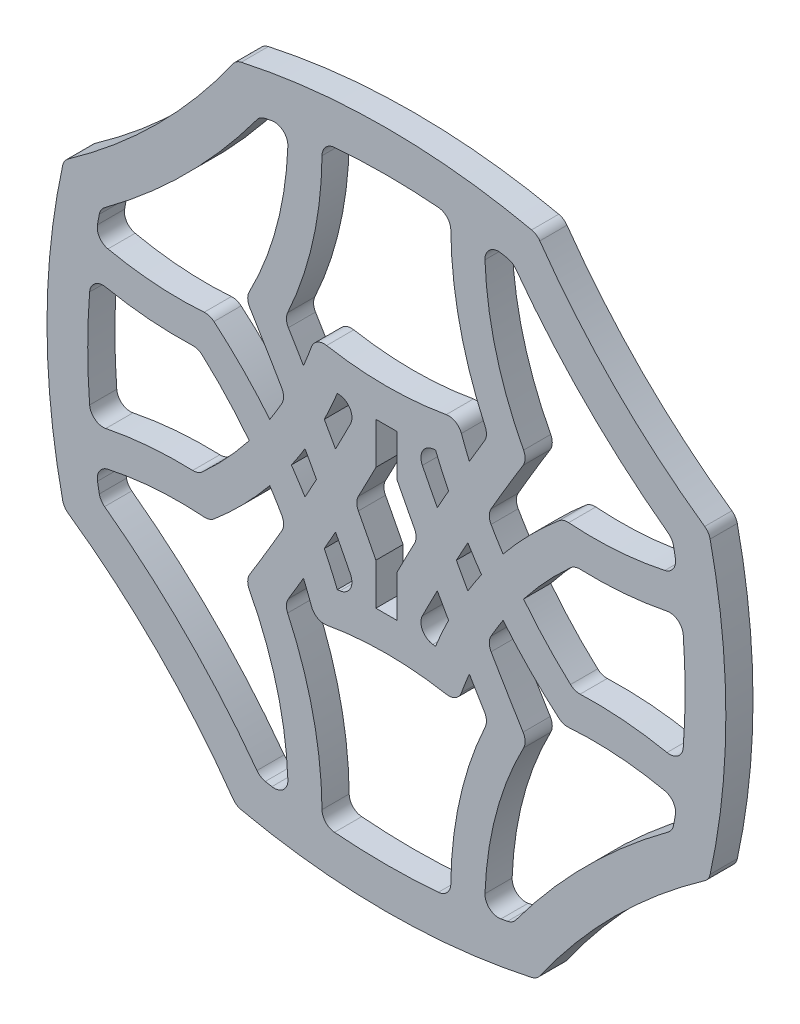
SolidWorks part; units mm, degrees
ref_plane "前视基准面" through (0, 0, 0) normal (0, 0, 1) x (1, 0, 0)
ref_plane "上视基准面" through (0, 0, 0) normal (0, 1, 0) x (1, 0, 0)
ref_plane "右视基准面" through (0, 0, 0) normal (1, 0, 0) x (0, 0, -1)
sketch "草图1" plane through (0, 0, 0) normal (0, 0, 1) x (1, 0, 0)
  line L0 (-3.1552, 0) -> (4.9138, 0) construction
  line L1 (0, 3.8534) -> (0, -1.8879) construction
  line L2 (0.0911, -0.0425) -> (-46.1387, 21.5148) construction
  line L4 (1.55, 12.05) -> (-1.55, 12.05)
  line L5 (1.55, 12.05) -> (1.55, 5.9226)
  line L6 (1.55, -12.05) -> (-1.55, -12.05)
  line L7 (-1.55, 12.05) -> (-1.55, 5.9226)
  line L8 (1.6505, -2.8587) -> (-5.8196, 10.0798) construction
  line L9 (-1.55, 0.7228) -> (-1.55, 0) construction
  line L10 (-1.55, -5.9226) -> (-1.55, -12.05)
  line L11 (-1.55, 2.6847) -> (-1.55, 0.7228) construction
  line L12 (-1.55, 0) -> (-1.55, -5.9226) construction
  line L13 (1.55, -0.7228) -> (1.55, -2.6847) construction
  line L14 (1.55, -5.9226) -> (1.55, -12.05)
  line L15 (1.55, -2.6847) -> (1.55, -5.9226) construction
  line L16 (1.55, 0) -> (1.55, -0.7228) construction
  line L17 (1.55, 5.9226) -> (1.55, 0) construction
  line L18 (-1.55, 5.9226) -> (-1.55, 2.6847) construction
  arc A106 (-22.1564, 47.5146) -> (22.1564, 47.5146) centre (0, -50) cw
  arc A107 (47.5146, 22.1564) -> (47.5146, -22.1564) centre (-50, 0) cw
  arc A108 (22.1564, -47.5146) -> (-22.1564, -47.5146) centre (0, 50) cw
  arc A109 (-47.5146, -22.1564) -> (-47.5146, 22.1564) centre (50, 0) cw
  arc A110 (22.1564, 47.5146) -> (47.5146, 22.1564) centre (104.4001, 104.4001) ccw
  arc A111 (47.5146, -22.1564) -> (22.1564, -47.5146) centre (104.4001, -104.4001) ccw
  arc A112 (-22.1564, -47.5146) -> (-47.5146, -22.1564) centre (-104.4001, -104.4001) ccw
  arc A113 (-47.5146, 22.1564) -> (-22.1564, 47.5146) centre (-104.4001, 104.4001) ccw
  arc A114 (-18.6124, 42.1389) -> (-14.4889, 42.8766) centre (0, -50) cw
  arc A115 (42.1389, 18.6124) -> (42.876, 14.4931) centre (-50, 0) cw
  arc A116 (18.6124, -42.1389) -> (14.4889, -42.8766) centre (0, 50) cw
  arc A117 (-42.1389, -18.6124) -> (-42.876, -14.4931) centre (50, 0) cw
  arc A118 (18.6124, 42.1389) -> (42.1389, 18.6124) centre (104.4001, 104.4001) ccw
  arc A119 (42.1389, -18.6124) -> (18.6124, -42.1389) centre (104.4001, -104.4001) ccw
  arc A120 (-18.6124, -42.1389) -> (-42.1389, -18.6124) centre (-104.4001, -104.4001) ccw
  arc A121 (-42.1389, 18.6124) -> (-18.6124, 42.1389) centre (-104.4001, 104.4001) ccw
  arc A122 (10.4858, 18.1619) -> (-10.4858, 18.1619) centre (0, 67.05) cw
  arc A123 (7.2328, 12.5277) -> (4, 12.1956) centre (0, 67.05) cw
  arc A124 (7.2328, -12.5277) -> (4, -12.1956) centre (0, -67.05) ccw
  arc A125 (10.4858, -18.1619) -> (-10.4858, -18.1619) centre (0, -67.05) ccw
  arc A126 (-10.4858, 18.1619) -> (-12.2188, 13.5572) centre (-67.5025, 36.9924) cw
  arc A127 (-7.2328, 12.5277) -> (-9.1545, 8.244) centre (-67.5025, 36.9924) cw
  arc A128 (-43.5187, -9.5) -> (-27.7384, -8) centre (-30.4783, -62.9317) cw
  arc A129 (-26.0438, -13.1288) -> (-42.876, -14.4931) centre (-30.4783, -62.9317) ccw
  arc A130 (-26.0438, 13.1288) -> (-42.876, 14.4931) centre (-30.4783, 62.9317) cw
  arc A131 (-43.5187, 9.5) -> (-27.7384, 8) centre (-30.4783, 62.9317) ccw
  arc A132 (-7.2328, -12.5277) -> (-9.1545, -8.244) centre (-67.5025, -36.9924) ccw
  arc A133 (-10.4858, -18.1619) -> (-12.2188, -13.5572) centre (-67.5025, -36.9924) ccw
  arc A134 (-20.2049, 0) -> (-27.7384, -8) centre (-67.5025, 36.9924) cw
  arc A135 (-17.1843, 4.2269) -> (-26.0438, 13.1288) centre (-67.5025, -36.9924) ccw
  arc A136 (-20.2049, 0) -> (-27.7384, 8) centre (-67.5025, -36.9924) ccw
  arc A137 (-17.1843, -4.2269) -> (-26.0438, -13.1288) centre (-67.5025, 36.9924) cw
  arc A138 (10.4858, 18.1619) -> (12.2188, 13.5572) centre (67.5025, 36.9924) ccw
  arc A139 (7.2328, 12.5277) -> (9.1545, 8.244) centre (67.5025, 36.9924) ccw
  arc A140 (7.2328, -12.5277) -> (9.1545, -8.244) centre (67.5025, -36.9924) cw
  arc A141 (10.4858, -18.1619) -> (12.2188, -13.5572) centre (67.5025, -36.9924) cw
  arc A142 (17.1843, 4.2269) -> (26.0438, 13.1288) centre (67.5025, -36.9924) cw
  arc A143 (20.2049, 0) -> (27.7384, 8) centre (67.5025, -36.9924) cw
  arc A144 (20.2049, 0) -> (27.7384, -8) centre (67.5025, 36.9924) ccw
  arc A145 (17.1843, -4.2269) -> (26.0438, -13.1288) centre (67.5025, 36.9924) ccw
  arc A146 (43.5187, -9.5) -> (27.7384, -8) centre (30.4783, -62.9317) ccw
  arc A147 (26.0438, -13.1288) -> (42.876, -14.4931) centre (30.4783, -62.9317) cw
  arc A148 (43.5187, 9.5) -> (27.7384, 8) centre (30.4783, 62.9317) cw
  arc A149 (26.0438, 13.1288) -> (42.876, 14.4931) centre (30.4783, 62.9317) ccw
  arc A150 (-43.5187, 9.5) -> (-42.876, 14.4931) centre (50, 0) cw construction
  arc A151 (-42.876, 14.4931) -> (-42.1389, 18.6124) centre (50, 0) cw
  arc A152 (-42.876, -14.4931) -> (-43.5187, -9.5) centre (50, 0) cw construction
  arc A153 (-43.5187, -9.5) -> (-43.5187, 9.5) centre (50, 0) cw
  arc A154 (43.5187, -9.5) -> (42.876, -14.4931) centre (-50, 0) cw construction
  arc A155 (42.876, -14.4931) -> (42.1389, -18.6124) centre (-50, 0) cw
  arc A156 (42.876, 14.4931) -> (43.5187, 9.5) centre (-50, 0) cw construction
  arc A157 (43.5187, 9.5) -> (43.5187, -9.5) centre (-50, 0) cw
  arc A158 (-4, -12.1956) -> (-7.5, -5.2865) centre (-326.3267, -171.1366) ccw
  arc A159 (-1.55, -5.9226) -> (-4.6315, 0) centre (-326.3267, -171.1366) ccw
  arc A160 (-15, 18.2077) -> (-9.5, 43.5187) centre (-64.4845, 42.2136) ccw
  arc A161 (-20.7386, 18) -> (-14.4889, 42.8766) centre (-64.4845, 42.2136) ccw
  arc A162 (1.55, -5.9226) -> (4.6315, 0) centre (326.3267, -171.1366) cw
  arc A163 (4, -12.1956) -> (7.5, -5.2865) centre (326.3267, -171.1366) cw
  arc A164 (20.7386, 18) -> (14.4889, 42.8766) centre (64.4845, 42.2136) cw
  arc A165 (15, 18.2077) -> (9.5, 43.5187) centre (64.4845, 42.2136) cw
  arc A166 (20.7386, -18) -> (14.4889, -42.8766) centre (64.4845, -42.2136) ccw
  arc A167 (15, -18.2077) -> (9.5, -43.5187) centre (64.4845, -42.2136) ccw
  arc A168 (4, 12.1956) -> (7.5, 5.2865) centre (326.3267, 171.1366) ccw
  arc A169 (1.55, 5.9226) -> (4.6315, 0) centre (326.3267, 171.1366) ccw
  arc A170 (-1.55, 5.9226) -> (-4.6315, 0) centre (-326.3267, 171.1366) cw
  arc A171 (-4, 12.1956) -> (-7.5, 5.2865) centre (-326.3267, 171.1366) cw
  arc A172 (-20.7386, -18) -> (-14.4889, -42.8766) centre (-64.4845, -42.2136) cw
  arc A173 (-15, -18.2077) -> (-9.5, -43.5187) centre (-64.4845, -42.2136) cw
  arc A174 (-14.4889, 42.8766) -> (-9.5, 43.5187) centre (0, -50) cw construction
  arc A175 (-9.5, 43.5187) -> (9.5, 43.5187) centre (0, -50) cw
  arc A176 (9.5, 43.5187) -> (14.4889, 42.8766) centre (0, -50) cw construction
  arc A177 (14.4889, 42.8766) -> (18.6124, 42.1389) centre (0, -50) cw
  arc A178 (-9.5, -43.5187) -> (-14.4889, -42.8766) centre (0, 50) cw construction
  arc A179 (-14.4889, -42.8766) -> (-18.6124, -42.1389) centre (0, 50) cw
  arc A180 (14.4889, -42.8766) -> (9.5, -43.5187) centre (0, 50) cw construction
  arc A181 (9.5, -43.5187) -> (-9.5, -43.5187) centre (0, 50) cw
  arc A182 (-11.995, -3.0826) -> (-14, 0) centre (-67.5025, -36.9924) ccw
  arc A183 (-14.8472, -8.1321) -> (-17.1843, -4.2269) centre (-67.5025, -36.9924) ccw
  arc A184 (-14.8472, -8.1321) -> (-20.7386, -18) centre (-326.3267, 171.1366) cw
  arc A185 (-12.2188, -13.5572) -> (-15, -18.2077) centre (-326.3267, 171.1366) cw
  arc A186 (12.2188, -13.5572) -> (15, -18.2077) centre (326.3267, 171.1366) ccw
  arc A187 (14.8472, -8.1321) -> (20.7386, -18) centre (326.3267, 171.1366) ccw
  arc A188 (11.995, -3.0826) -> (14, 0) centre (67.5025, -36.9924) cw
  arc A189 (14.8472, -8.1321) -> (17.1843, -4.2269) centre (67.5025, -36.9924) cw
  arc A190 (11.995, 3.0826) -> (14, 0) centre (67.5025, 36.9924) ccw
  arc A191 (14.8472, 8.1321) -> (20.7386, 18) centre (326.3267, -171.1366) cw
  arc A192 (12.2188, 13.5572) -> (15, 18.2077) centre (326.3267, -171.1366) cw
  arc A193 (14.8472, 8.1321) -> (17.1843, 4.2269) centre (67.5025, 36.9924) ccw
  arc A194 (-14.8472, 8.1321) -> (-17.1843, 4.2269) centre (-67.5025, 36.9924) cw
  arc A195 (-14.8472, 8.1321) -> (-20.7386, 18) centre (-326.3267, -171.1366) ccw
  arc A196 (-12.2188, 13.5572) -> (-15, 18.2077) centre (-326.3267, -171.1366) ccw
  arc A197 (-11.995, 3.0826) -> (-14, 0) centre (-67.5025, 36.9924) cw
  arc A198 (-10.3061, 0) -> (-11.995, -3.0826) centre (-326.3267, 171.1366) cw
  arc A199 (-10.3061, 0) -> (-11.995, 3.0826) centre (-326.3267, -171.1366) ccw
  arc A200 (-7.5, -5.2865) -> (-9.1545, -8.244) centre (-326.3267, 171.1366) cw
  arc A201 (-7.5, 5.2865) -> (-9.1545, 8.244) centre (-326.3267, -171.1366) ccw
  arc A202 (10.3061, 0) -> (11.995, -3.0826) centre (326.3267, 171.1366) ccw
  arc A203 (7.5, 5.2865) -> (9.1545, 8.244) centre (326.3267, -171.1366) cw
  arc A204 (7.5, -5.2865) -> (9.1545, -8.244) centre (326.3267, 171.1366) ccw
  arc A205 (10.3061, 0) -> (11.995, 3.0826) centre (326.3267, -171.1366) cw
  arc A206 (-4, 12.1956) -> (-7.2328, 12.5277) centre (0, 67.05) cw
  arc A207 (-4, -12.1956) -> (-7.2328, -12.5277) centre (0, -67.05) ccw
  point P10 (-50, 0)
  point P11 (50, 0)
  point P20 (0, 0)
  point P31 (0, 0)
  point P42 (0, 0)
  point P53 (0, 0)
  dimension "D6" = 4
  dimension "D7" = 4
  dimension "D10" = 24.1
  dimension "D11" = 5
  dimension "D5" = 100
  dimension "D12" = 5
  dimension "D13" = 3.1
  dimension "D14" = 5
  dimension "D15" = 19
  dimension "D17" = 50
  dimension "D18" = 50
  dimension "D8" = 6
  dimension "D9" = 6
  dimension "D21" = 5
  dimension "D22" = 5
  dimension "D23" = 50
  dimension "D1" = 4
  dimension "D2" = 4
  dimension "D3" = 100
  dimension "D16" = 30
  dimension "D19" = 28
  dimension "D4" = 25
  dimension "D20" = 16
  dimension "D24" = 19
  dimension "D25" = 18
  dimension "30" = 30
  dimension "D26" = 8
  dimension "D27" = 15
extrude "凸台-拉伸2" add sketch "草图1" along normal blind 4 contours A113 A109 A112 A108 A111 A107 A110 A106 A140 A124 A132 A127 A123 A139 A130 A151 A121 A114 A118 A115 A149 A142 A138 A122 A126 A135 A128 A153 A131 A136 A134 A147 A155 A119 A116 A120 A117 A129 A137 A133 A125 A141 A145 A148
fillet "圆角1" radius 2 62 edges at (-4, -12.1956, 2) (4, -12.1956, 2) (4, 12.1956, 2) (-4, 12.1956, 2) (15, 18.2077, 2) (-15, 18.2077, 2) (-27.7384, 8, 2) (27.7384, 8, 2) (27.7384, -8, 2) (-27.7384, -8, 2) (-15, -18.2077, 2) (15, -18.2077, 2) (-14.8472, -8.1321, 2) (-14.8472, 8.1321, 2) (14.8472, -8.1321, 2) (14.8472, 8.1321, 2) (14.4889, 42.8766, 2) (-14.4889, 42.8766, 2) (9.5, 43.5187, 2) (-9.5, 43.5187, 2) (42.876, 14.4931, 2) (43.5187, 9.5, 2) (43.5187, -9.5, 2) (42.876, -14.4931, 2) (14.4889, -42.8766, 2) (9.5, -43.5187, 2) (-9.5, -43.5187, 2) (-14.4889, -42.8766, 2) (-42.876, -14.4931, 2) (-43.5187, -9.5, 2) (-43.5187, 9.5, 2) (-42.876, 14.4931, 2) (-4.6315, 0, 2) (4.6315, 0, 2) (26.0438, 13.1288, 2) (20.7386, 18, 2) (-20.7386, 18, 2) (-26.0438, 13.1288, 2) (-20.7386, -18, 2) (-26.0438, -13.1288, 2) (26.0438, -13.1288, 2) (20.7386, -18, 2) (-10.4858, -18.1619, 2) (10.4858, -18.1619, 2) (-10.4858, 18.1619, 2) (10.4858, 18.1619, 2) (-42.1389, 18.6124, 2) (-18.6124, 42.1389, 2) (18.6124, 42.1389, 2) (42.1389, 18.6124, 2) (42.1389, -18.6124, 2) (18.6124, -42.1389, 2) (-42.1389, -18.6124, 2) (-18.6124, -42.1389, 2) (47.5146, -22.1564, 2) (22.1564, -47.5146, 2) (-22.1564, -47.5146, 2) (-47.5146, -22.1564, 2) (-47.5146, 22.1564, 2) (-22.1564, 47.5146, 2) (47.5146, 22.1564, 2) (22.1564, 47.5146, 2)
